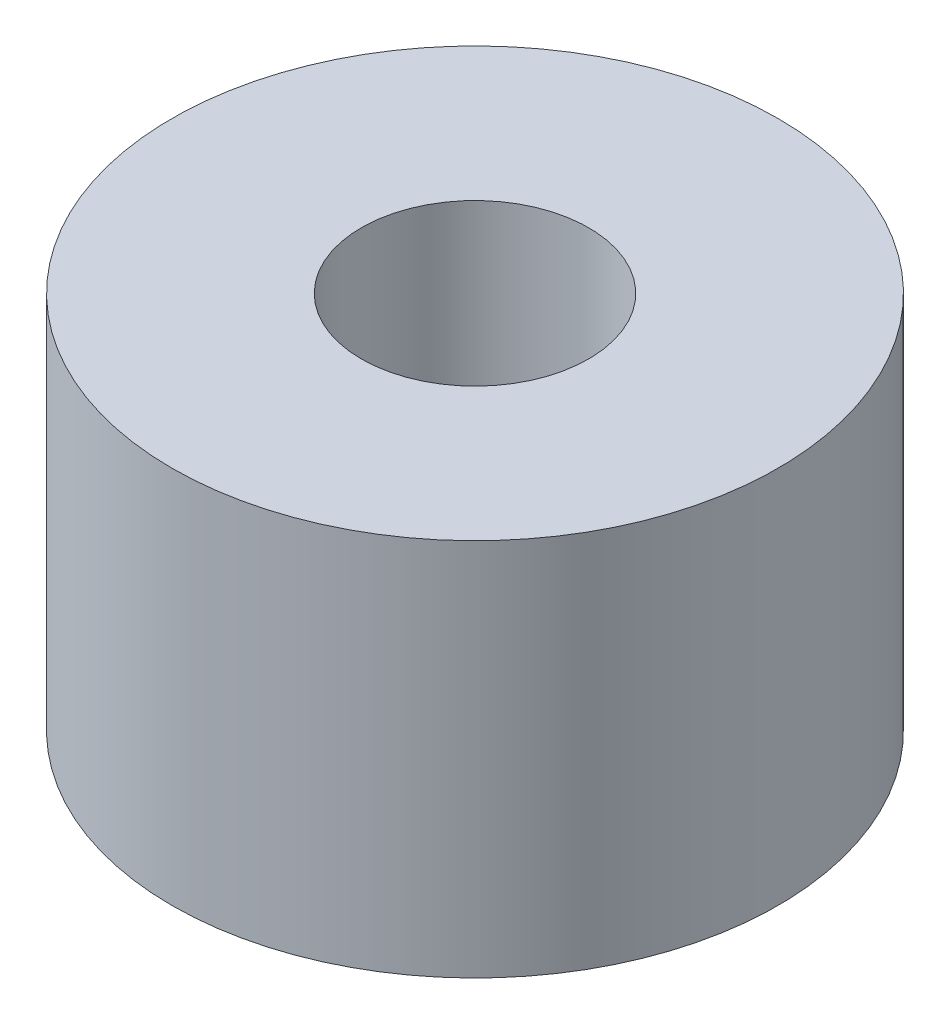
SolidWorks part; units mm, degrees
ref_plane "Front Plane" through (0, 0, 0) normal (0, 0, 1) x (1, 0, 0)
ref_plane "Top Plane" through (0, 0, 0) normal (0, 1, 0) x (1, 0, 0)
ref_plane "Right Plane" through (0, 0, 0) normal (1, 0, 0) x (0, 0, -1)
sketch "Sketch1" plane through (0, 0, 0) normal (0, 1, 0) x (1, 0, 0)
  circle A0 centre (0, 0) radius 8
  circle A1 centre (0, 0) radius 3.002
extrude "Boss-Extrude1" add sketch "Sketch1" along normal blind 10
